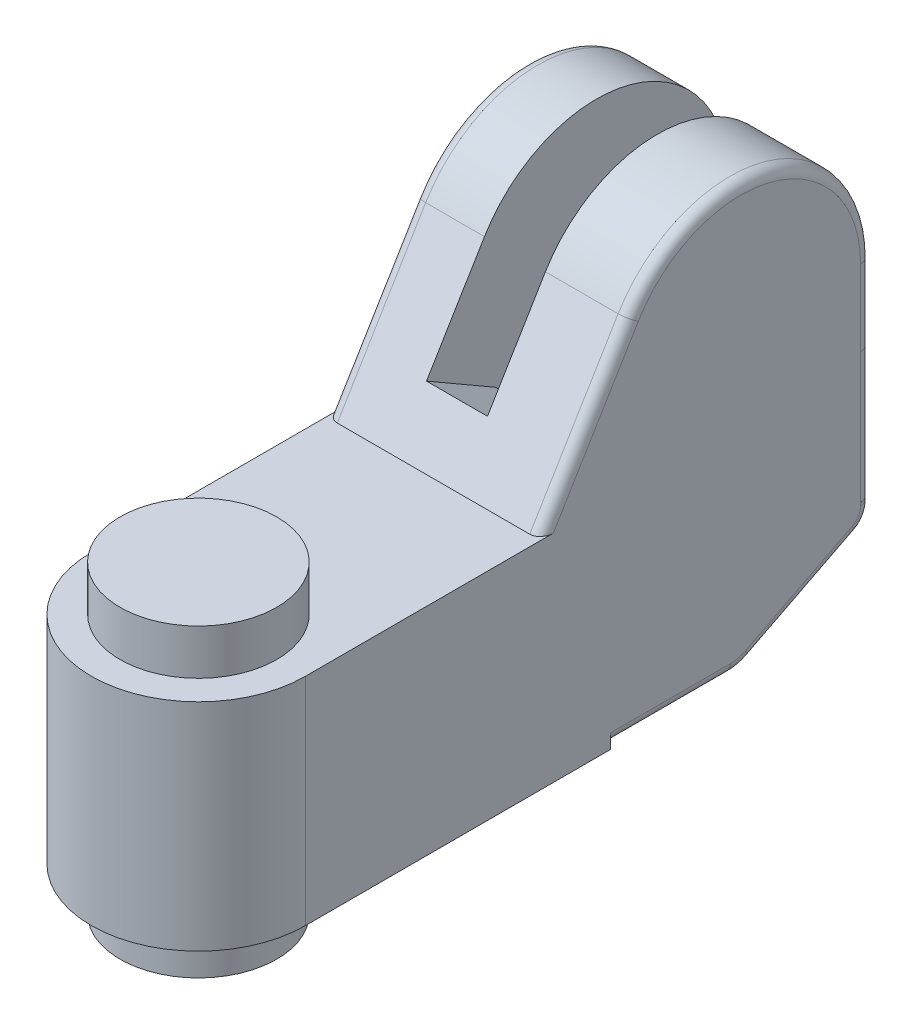
SolidWorks part; units mm, degrees
ref_plane "Front" through (0, 0, 0) normal (0, 0, 1) x (1, 0, 0)
ref_plane "Top" through (0, 0, 0) normal (0, 1, 0) x (1, 0, 0)
ref_plane "Right" through (0, 0, 0) normal (1, 0, 0) x (0, 0, -1)
sketch "Sketch1" plane through (0, 0, 0) normal (1, 0, 0) x (0, 0, -1)
  line L0 (-12.3, 0) -> (35, 0)
  line L1 (35, 0) -> (35, 0.4)
  line L2 (35, 0.4) -> (48.7996, 0.4)
  line L3 (51.0696, 0.945) -> (63.362, 7.2083)
  line L4 (65, 9.8813) -> (65, 33.9)
  line L5 (37.1535, 41.6439) -> (27, 24.8)
  line L6 (27, 24.8) -> (-12.3, 24.8)
  line L7 (-12.3, 24.8) -> (-12.3, 0)
  line L8 (48.7996, 0.4) -> (50, 0.4) construction
  line L9 (50, 0.4) -> (51.0696, 0.945) construction
  arc A0 (48.7996, 0.4) -> (51.0696, 0.945) centre (48.7996, 5.4) ccw
  arc A1 (63.362, 7.2083) -> (65, 9.8813) centre (62, 9.8813) ccw
  arc A2 (65, 33.9) -> (37.1535, 41.6439) centre (50, 33.9) ccw
  dimension "D5" = 5
  dimension "D6" = 15
  dimension "D7" = 3
  dimension "D1" = 77.3
  dimension "D2" = 12.3
  dimension "D3" = 35
  dimension "D4" = 0.4
  dimension "D8" = 153
  dimension "D9" = 15
  dimension "D10" = 33.5
  dimension "D11" = 24.8
  dimension "D12" = 38
extrude "Boss-Extrude1" add sketch "Sketch1" along normal mid plane 24.6
sketch "Sketch2" plane through (0, 24.8, 0) normal (0, 1, 0) x (1, 0, 0)
  line L0 (-12.3, 27) -> (-12.3, -12.3) construction
  line L1 (12.3, 27) -> (12.3, -12.3) construction
  line L2 (-12.3, 0) -> (12.3, 0) construction
  line L3 (-12.3, 0) -> (-12.3, -13.3)
  line L4 (-12.3, -13.3) -> (12.3, -13.3)
  line L5 (12.3, -13.3) -> (12.3, 0)
  line L6 (12.3, -12.3) -> (-12.3, -12.3) construction
  arc A0 (-12.3, 0) -> (12.3, 0) centre (0, 0) ccw
  dimension "D1" = 1
extrude "Cut-Extrude1" cut sketch "Sketch2" against normal through all
sketch "Sketch3" plane through (0, 0, 0) normal (0, -1, 0) x (1, 0, 0)
  circle A0 centre (0, 0) radius 9
  dimension "D1" = 18
extrude "Boss-Extrude2" add sketch "Sketch3" along normal blind 5 and the other way blind 30
sketch "Sketch4" plane through (-12.3, 0, 0) normal (-1, 0, 0) x (0, 0, 1)
  line L0 (-38.4277, 26.0208) -> (-30.4962, 30.6)
  line L1 (-37.1535, 41.6439) -> (-27, 24.8) construction
  line L2 (-63.8, 22.0069) -> (-65, 22.0069)
  line L3 (-65, 9.8813) -> (-65, 33.9) construction
  line L4 (-38.4277, 26.0208) -> (-27.7359, 26.0208) construction
  line L5 (-65, 22.0069) -> (-65, 33.9)
  line L6 (-37.1535, 41.6439) -> (-30.4962, 30.6)
  arc A0 (-63.8, 22.0069) -> (-54.9412, 20.801) centre (-62, 2.0881) cw
  arc A1 (-54.9412, 20.801) -> (-38.4277, 26.0208) centre (-50, 33.9) ccw
  arc A2 (-37.1535, 41.6439) -> (-65, 33.9) centre (-50, 33.9) ccw construction
  arc A3 (-37.1535, 41.6439) -> (-65, 33.9) centre (-50, 33.9) ccw
  dimension "D1" = 14
  dimension "D3" = 20
  dimension "D2" = 1.2
  dimension "D4" = 30
  dimension "D5" = 3.3
  dimension "D6" = 12
extrude "Cut-Extrude2" cut sketch "Sketch4" against normal blind 7 from offset 8 offset against normal yes
sketch "Sketch5" plane through (2.7, 0, 0) normal (-1, 0, 0) x (0, 0, 1)
  circle A0 centre (-50, 33.9) radius 5
  dimension "D1" = 10
extrude "Cut-Extrude3" cut sketch "Sketch5" against normal blind 7 and the other way blind 14
sketch "Sketch6" plane through (-12.3, 0, 0) normal (-1, 0, 0) x (0, 0, 1)
  line L0 (-35, 0.4) -> (-35, 14.4)
  line L1 (-35, 14.4) -> (-41, 14.4)
  line L2 (-43, 16.4) -> (-43, 33.9)
  line L3 (-57, 33.9) -> (-57, 3.9667)
  line L4 (-51.0696, 0.945) -> (-63.362, 7.2083) construction
  line L5 (-35.01, 0.4) -> (-35.01, 14.39)
  line L6 (-35.01, 14.39) -> (-41, 14.39)
  line L7 (-43.01, 16.4) -> (-43.01, 33.9)
  line L8 (-56.99, 33.9) -> (-56.99, 3.9616)
  line L9 (-35.01, 0.4) -> (-35, 0.4)
  line L10 (-56.99, 33.9) -> (-56.99, 3.9667) construction
  line L11 (-57, 3.9667) -> (-56.99, 3.9616)
  arc A0 (-41, 14.4) -> (-43, 16.4) centre (-41, 16.4) cw
  arc A1 (-43, 33.9) -> (-57, 33.9) centre (-50, 33.9) ccw
  arc A2 (-37.1535, 41.6439) -> (-65, 33.9) centre (-50, 33.9) ccw construction
  arc A3 (-41, 14.39) -> (-43.01, 16.4) centre (-41, 16.4) cw
  arc A4 (-43.01, 33.9) -> (-56.99, 33.9) centre (-50, 33.9) ccw
  dimension "D1" = 7
  dimension "D3" = 2
  dimension "D2" = 14
  dimension "D4" = 0.01
extrude "Cut-Extrude4" cut sketch "Sketch6" against normal blind 1.25
fillet "Fillet1" radius 1.25 15 edges at (12.3, 0.4, -41.8998) (12.3, 0.5382, -49.9668) (12.3, 4.0766, -57.2158) (12.3, 8.3138, -64.5579) (12.3, 33.2219, -32.0768) (12.3, 48.3516, -54.0189) (-12.3, 33.2219, -32.0768) (-12.3, 48.3516, -54.0189) (-12.3, 21.8906, -65) (-12.3, 8.3138, -64.5579) (-12.3, 2.4533, -54.0298) (-12.3, 0.5382, -49.9668) (12.3, 21.8906, -65) (-12.3, 5.5875, -60.181) (-12.3, 0.4, -41.9048)
sketch "Sketch8" plane through (0, 0, -65) normal (0, 0, -1) x (-1, 0, 0)
  line L0 (-4.7, 16.6) -> (6.3, 16.6) construction
  line L1 (-4.1226, 15.6) -> (-3.5453, 16.6)
  line L2 (-3.5453, 16.6) -> (-4.1226, 17.6)
  line L3 (-4.1226, 17.6) -> (-5.2774, 17.6)
  line L4 (-5.2774, 17.6) -> (-5.8547, 16.6)
  line L5 (-5.8547, 16.6) -> (-5.2774, 15.6)
  line L6 (-5.2774, 15.6) -> (-4.1226, 15.6)
  line L7 (6.8774, 15.6) -> (7.4547, 16.6)
  line L8 (7.4547, 16.6) -> (6.8774, 17.6)
  line L9 (6.8774, 17.6) -> (5.7226, 17.6)
  line L10 (5.7226, 17.6) -> (5.1453, 16.6)
  line L11 (5.1453, 16.6) -> (5.7226, 15.6)
  line L12 (5.7226, 15.6) -> (6.8774, 15.6)
  line L13 (0.8, 16.6) -> (0.8, 4) construction
  line L14 (0.8, 16.6) -> (0.8, 22.0069) construction
  line L15 (-9, 0) -> (9, 0) construction
  line L16 (-2.7, 22.0069) -> (4.3, 22.0069) construction
  circle A0 centre (0.8, 4) radius 3.2
  circle A1 centre (-4.7, 16.6) radius 1 construction
  circle A2 centre (6.3, 16.6) radius 1 construction
  dimension "D1" = 2
  dimension "D5" = 6.4
  dimension "D2" = 11
  dimension "D3" = 12.6
  dimension "D4" = 4
extrude "Cut-Extrude6" cut sketch "Sketch8" against normal blind 25.9
sketch "Sketch7" plane through (0, 0, -65) normal (0, 0, -1) x (-1, 0, 0)
  line L0 (-12.3, 9.8813) -> (-12.3, 33.9) construction
  line L1 (-12.3, 10.21) -> (12.3, 10.21)
  line L2 (-12.3, 10.21) -> (-12.3, 10.2)
  line L3 (-12.3, 10.2) -> (12.3, 10.2)
  line L4 (12.3, 10.21) -> (12.3, 10.2)
  line L5 (12.3, 33.9) -> (12.3, 9.8813) construction
  line L7 (-12.3, 25.2) -> (12.3, 25.2)
  line L8 (-12.3, 25.2) -> (-12.3, 25.19)
  line L9 (-12.3, 25.19) -> (-2.71, 25.19)
  line L12 (4.3, 33.9) -> (4.3, 22.0069) construction
  line L13 (-2.71, 25.19) -> (-2.71, 21.9969)
  line L14 (-2.71, 21.9969) -> (4.31, 21.9969)
  line L15 (4.31, 25.19) -> (4.31, 21.9969)
  line L16 (-2.7, 33.9) -> (-2.7, 22.0069) construction
  line L17 (-2.7, 22.0069) -> (4.3, 22.0069) construction
  line L18 (4.31, 25.19) -> (12.3, 25.19)
  line L19 (12.3, 25.2) -> (12.3, 25.19)
  line L20 (-11.05, 0.4) -> (11.05, 0.4) construction
  line L21 (-4.7, 16.6) -> (6.3, 16.6) construction
  line L22 (6.3, 16.6) -> (6.3, 17.6) construction
  line L23 (6.8774, 17.6) -> (5.7226, 17.6) construction
  circle A0 centre (-4.7, 16.6) radius 1.5
  circle A1 centre (6.3, 16.6) radius 1.5
  dimension "D9" = 3
  dimension "D1" = 0.01
  dimension "D2" = 0.01
  dimension "D3" = 0.01
  dimension "D4" = 0.01
  dimension "D5" = 15
  dimension "D6" = 0.01
  dimension "D7" = 9.8
  dimension "D8" = 11
  dimension "D10" = 1
extrude "Cut-Extrude5" cut sketch "Sketch7" against normal blind 1.25
sketch "Sketch9" plane through (0, 0, -39.1) normal (0, 0, -1) x (-1, 0, 0)
  line L1 (1.3774, 5) -> (0.2226, 5)
  line L2 (0.2226, 5) -> (-0.3547, 4)
  line L3 (-0.3547, 4) -> (0.2226, 3)
  line L4 (0.2226, 3) -> (1.3774, 3)
  line L5 (1.3774, 3) -> (1.9547, 4)
  line L6 (1.9547, 4) -> (1.3774, 5)
  circle A0 centre (0.8, 4) radius 2.75
  circle A1 centre (0.8, 4) radius 1 construction
  dimension "D1" = 5.5
  dimension "D2" = 2
extrude "Boss-Extrude3" add sketch "Sketch9" along normal blind 2
chamfer "Chamfer1" distance 0.25 angle 45 1 edges at (-0.8, 6.75, -41.1)
sketch "Sketch10" plane through (0, 0, -65) normal (0, 0, -1) x (-1, 0, 0)
  line L0 (0.8, 16.6) -> (0.8, 21.9969) construction
  line L1 (-8.2, 11.6) -> (9.8, 11.6) construction
  line L2 (-8.2, 11.6) -> (-8.2, 21.6) construction
  line L3 (-8.2, 21.6) -> (9.8, 21.6) construction
  line L4 (9.8, 11.6) -> (9.8, 21.6) construction
  line L5 (-8.2, 11.6) -> (9.8, 21.6) construction
  line L6 (-8.2, 21.6) -> (9.8, 11.6) construction
  line L7 (-2.71, 21.9969) -> (4.31, 21.9969) construction
  line L8 (6.3, 16.6) -> (-4.7, 16.6) construction
  circle A0 centre (-8.2, 21.6) radius 1.25
  circle A1 centre (9.8, 21.6) radius 1.25
  circle A2 centre (9.8, 11.6) radius 1.25
  circle A3 centre (-8.2, 11.6) radius 1.25
  point P0 (0.8, 16.6)
  dimension "D3" = 2.5
  dimension "D1" = 10
  dimension "D2" = 18
extrude "Cut-Extrude7" cut sketch "Sketch10" against normal blind 0.1 draft 45
sketch "Sketch11" plane through (0, 0, -64.9) normal (0, 0, -1) x (-1, 0, 0)
  line L0 (10, 22.7325) -> (10, 20.4675)
  line L1 (-8.4, 22.7325) -> (-8, 22.7325)
  line L2 (-8.4, 22.7325) -> (-8.4, 20.4675)
  line L3 (-8.4, 20.4675) -> (-8, 20.4675)
  line L4 (-8, 22.7325) -> (-8, 20.4675)
  line L5 (9.6, 20.4675) -> (10, 20.4675)
  line L6 (9.6, 22.7325) -> (9.6, 20.4675)
  line L7 (9.6, 22.7325) -> (10, 22.7325)
  line L8 (-8, 12.7325) -> (-8, 10.4675)
  line L9 (-8.4, 10.4675) -> (-8, 10.4675)
  line L10 (-8.4, 12.7325) -> (-8.4, 10.4675)
  line L11 (-8.4, 12.7325) -> (-8, 12.7325)
  line L12 (10, 12.7325) -> (10, 10.4675)
  line L13 (9.6, 10.4675) -> (10, 10.4675)
  line L14 (9.6, 12.7325) -> (9.6, 10.4675)
  line L15 (9.6, 12.7325) -> (10, 12.7325)
  circle A0 centre (-8.2, 21.6) radius 1.15 construction
  circle A1 centre (9.8, 21.6) radius 1.15 construction
  circle A2 centre (9.8, 11.6) radius 1.15 construction
  circle A3 centre (-8.2, 11.6) radius 1.15 construction
  dimension "D1" = 0.4
  dimension "D2" = 2
  dimension "D3" = 2
extrude "Cut-Extrude8" cut sketch "Sketch11" against normal blind 0.2 draft 5
sketch "Sketch12" plane through (-12.3, 0, 0) normal (-1, 0, 0) x (0, 0, 1)
  line L0 (-40.5, 7.4) -> (-55, 7.4) construction
  line L1 (-35, 0) -> (-35, 14.4) construction
  line L2 (-35.01, 0.4) -> (-48.7996, 0.4) construction
  circle A0 centre (-55, 7.4) radius 1.75
  circle A1 centre (-40.5, 7.4) radius 1.75
  dimension "D1" = 3.5
  dimension "D2" = 5.5
  dimension "D3" = 14.5
  dimension "D4" = 7
extrude "Cut-Extrude9" cut sketch "Sketch12" against normal blind 0.1 draft 45
sketch "Sketch13" plane through (-12.2, 0, 0) normal (-1, 0, 0) x (0, 0, 1)
  line L0 (-55, 7.4) -> (-40.5, 7.4) construction
  line L2 (-42.131, 7.15) -> (-38.869, 7.15)
  line L3 (-42.131, 7.15) -> (-42.131, 7.65)
  line L4 (-42.131, 7.65) -> (-38.869, 7.65)
  line L5 (-38.869, 7.15) -> (-38.869, 7.65)
  line L6 (-42.131, 7.15) -> (-38.869, 7.65) construction
  line L7 (-42.131, 7.65) -> (-38.869, 7.15) construction
  line L8 (-56.631, 7.15) -> (-53.369, 7.15)
  line L9 (-56.631, 7.15) -> (-56.631, 7.65)
  line L10 (-56.631, 7.65) -> (-53.369, 7.65)
  line L11 (-53.369, 7.15) -> (-53.369, 7.65)
  line L12 (-56.631, 7.15) -> (-53.369, 7.65) construction
  line L13 (-56.631, 7.65) -> (-53.369, 7.15) construction
  circle A0 centre (-40.5, 7.4) radius 1.65 construction
  circle A1 centre (-55, 7.4) radius 1.65 construction
  dimension "D1" = 0.5
extrude "Cut-Extrude10" cut sketch "Sketch13" against normal blind 0.2 draft 5
